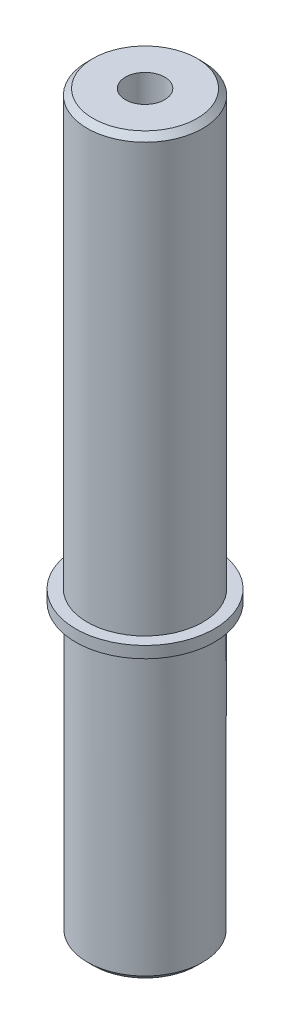
SolidWorks part; units mm, degrees
material "6061 Alloy"
ref_plane "Front Plane" through (0, 0, 0) normal (0, 0, 1) x (1, 0, 0)
ref_plane "Top Plane" through (0, 0, 0) normal (0, 1, 0) x (1, 0, 0)
ref_plane "Right Plane" through (0, 0, 0) normal (1, 0, 0) x (0, 0, -1)
sketch "Sketch1" plane through (0, 0, 0) normal (1, 0, 0) x (0, 0, -1)
  line L0 (0, 0) -> (0, 127)
  line L1 (0, 127) -> (-10, 127)
  line L2 (-10, 127) -> (-10, 52)
  line L3 (-10, 52) -> (-12, 52)
  line L4 (-12, 52) -> (-12, 50)
  line L5 (-12, 50) -> (-9.95, 50)
  line L6 (-9.95, 50) -> (-9.95, 0)
  line L7 (-9.95, 0) -> (0, 0)
  dimension "D1" = 9.95
  dimension "D2" = 10
  dimension "D3" = 2
  dimension "D4" = 12
  dimension "D5" = 50
  dimension "D6" = 75
revolve "Revolve1" add sketch "Sketch1" angle 360 about L0
chamfer "Chamfer1" distance 1 angle 45 2 edges at (0, 0, -9.95) (0, 127, -10)
hole_wizard "M8 Tapped Hole1" positions "Sketch2" profile "Sketch3" tap size "M8" standard "ISO" end condition through all
sketch "Sketch2" plane through (0, 127, 0) normal (0, 1, 0) x (1, 0, 0)
  point P0 (0, 0)
cosmetic thread "Hole Thread1" parameters "D1"=16, "D2"=8
sketch "Sketch3" plane through (0, 127, 0) normal (1, 0, 0) x (0, 0, 1)
  line L0 (0, 0) -> (0, 127)
  line L1 (0, 127) -> (3.4, 127)
  line L2 (3.4, 127) -> (3.4, 0)
  line L5 (3.4, 0) -> (0, 0)
  line L11 (0, -6.35) -> (0, 107.95) construction
  dimension "Thru Tap Drill Dia." = 6.8
  dimension "Thru Tap Drill Depth" = 127
